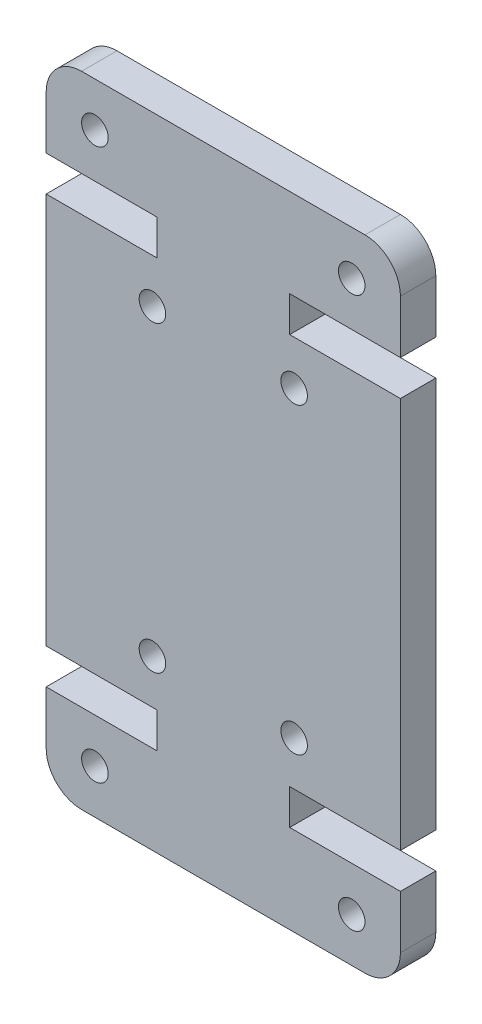
SolidWorks part; units mm, degrees
material "Acrylic (Medium-high impact)"
ref_plane "Front Plane" through (0, 0, 0) normal (0, 0, 1) x (1, 0, 0)
ref_plane "Top Plane" through (0, 0, 0) normal (0, 1, 0) x (1, 0, 0)
ref_plane "Right Plane" through (0, 0, 0) normal (1, 0, 0) x (0, 0, -1)
sketch "Model" plane through (0, 0, 0) normal (0, 0, 1) x (1, 0, 0)
  line L61 (2, 36.1) -> (18, 36.1)
  line L62 (0, 34.1) -> (0, 31.1)
  line L63 (20, 31.1) -> (20, 34.1)
  line L64 (6.25, 31.1) -> (0, 31.1)
  line L65 (13.75, 31.1) -> (20, 31.1)
  line L66 (6.25, 29.1) -> (0, 29.1)
  line L67 (13.75, 29.1) -> (20, 29.1)
  line L68 (6.25, 31.1) -> (6.25, 29.1)
  line L69 (13.75, 31.1) -> (13.75, 29.1)
  line L75 (2, 0) -> (18, 0)
  line L76 (0, 2) -> (0, 5)
  line L77 (20, 5) -> (20, 2)
  line L78 (6.25, 5) -> (0, 5)
  line L79 (13.75, 5) -> (20, 5)
  line L80 (6.25, 7) -> (0, 7)
  line L81 (13.75, 7) -> (20, 7)
  line L82 (6.25, 5) -> (6.25, 7)
  line L83 (13.75, 5) -> (13.75, 7)
  line L84 (0, 29.1) -> (0, 7)
  line L85 (20, 29.1) -> (20, 7)
  arc A23 (20, 34.1) -> (18, 36.1) centre (18, 34.1) ccw
  arc A24 (2, 36.1) -> (0, 34.1) centre (2, 34.1) ccw
  circle A27 centre (14, 26.6) radius 0.75
  circle A28 centre (6, 26.6) radius 0.75
  arc A31 (18, 0) -> (20, 2) centre (18, 2) ccw
  arc A32 (0, 2) -> (2, 0) centre (2, 2) ccw
  circle A33 centre (14, 9.5) radius 0.75
  circle A34 centre (6, 9.5) radius 0.75
  circle A35 centre (17.25, 2.5) radius 0.75
  circle A36 centre (2.75, 2.5) radius 0.75
  circle A63 centre (17.25, 33.6) radius 0.75
  circle A64 centre (2.75, 33.6) radius 0.75
  dimension "D1" = 1.5
  dimension "D2" = 2
  dimension "D3" = 20
  dimension "D4" = 2.75
  dimension "D5" = 3.25
  dimension "D6" = 0.25
  dimension "D7" = 36.1
  dimension "D8" = 0.25
  dimension "D9" = 3.25
  dimension "D10" = 2.5
  dimension "D11" = 2.5
  dimension "D12" = 2
  dimension "D13" = 2.5
  dimension "D14" = 17.1
  dimension "D15" = 2.5
extrude "Boss-Extrude1" add sketch "Model" along normal blind 2
